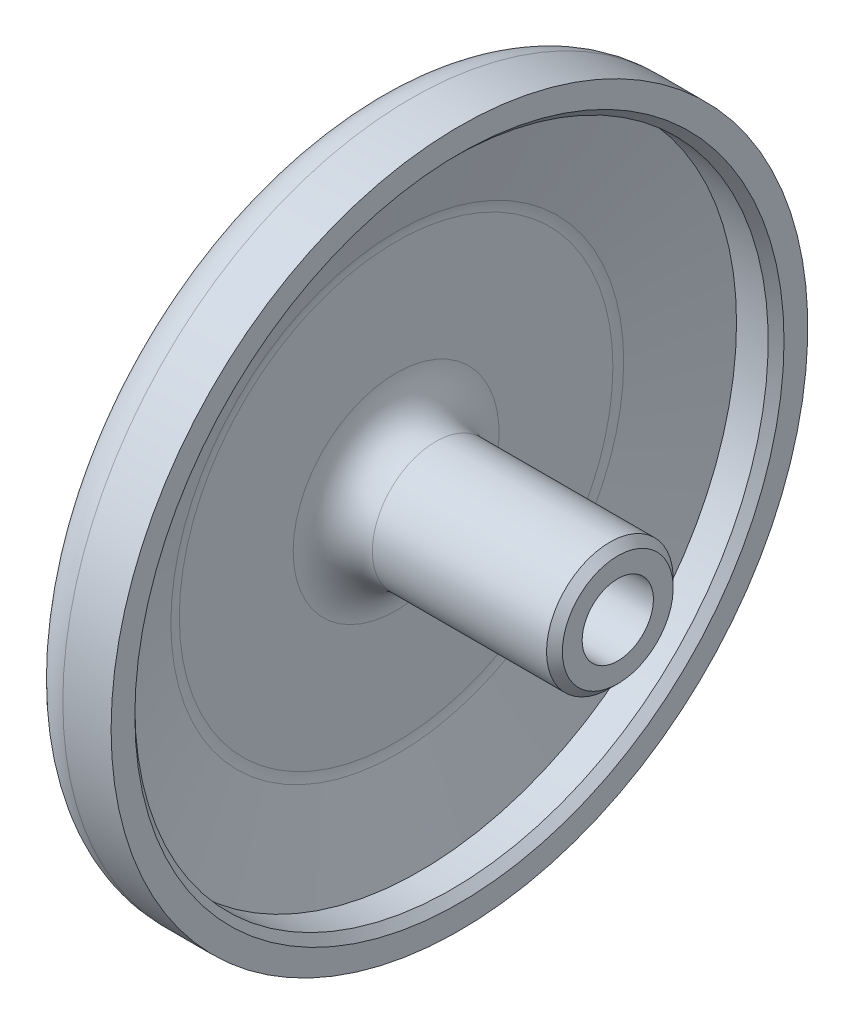
SolidWorks part; units mm, degrees
material "Plain Carbon Steel"
ref_plane "Front Plane" through (0, 0, 0) normal (0, 0, 1) x (1, 0, 0)
ref_plane "Top Plane" through (0, 0, 0) normal (0, 1, 0) x (1, 0, 0)
ref_plane "Right Plane" through (0, 0, 0) normal (1, 0, 0) x (0, 0, -1)
sketch "Sketch1" plane through (0, 0, 0) normal (0, 0, 1) x (1, 0, 0)
  line L0 (0, 0) -> (48.1781, 0) construction
  line L1 (4, 22) -> (4, 20)
  line L2 (4, 20) -> (1.5, 20)
  line L3 (1.5, 20) -> (0, 14)
  line L4 (0, 14) -> (0, 4)
  line L5 (0, 4) -> (14, 4)
  line L6 (14, 4) -> (14, 0)
  line L7 (14, 0) -> (-3, 0)
  line L8 (-3, 0) -> (-3, 14)
  line L9 (-3, 14) -> (-1, 22)
  line L10 (-1, 22) -> (4, 22)
  dimension "D1" = 20
  dimension "D2" = 2
  dimension "D3" = 4
  dimension "D4" = 3
  dimension "D5" = 2.5
  dimension "D6" = 4
  dimension "D7" = 10
  dimension "D8" = 14
revolve "Revolve1" add sketch "Sketch1" angle 360 about L0
fillet "Fillet1" radius 2.5 4 edges at (0, 0, 4) (-3, 0, 14) (-1, 0, 22) (0, 0, 14)
chamfer "Chamfer1" distance 0.5 angle 45 2 edges at (14, 0, 4) (4, 0, 20)
sketch "Sketch3" plane through (-3, 0, 0) normal (-1, 0, 0) x (0, 0, 1)
  circle A0 centre (0, 0) radius 2.25
  dimension "D1" = 4.5
extrude "Cut-Extrude1" cut sketch "Sketch3" against normal through all
chamfer "Chamfer2" distance 1 angle 45 1 edges at (-3, 0, 2.25)
